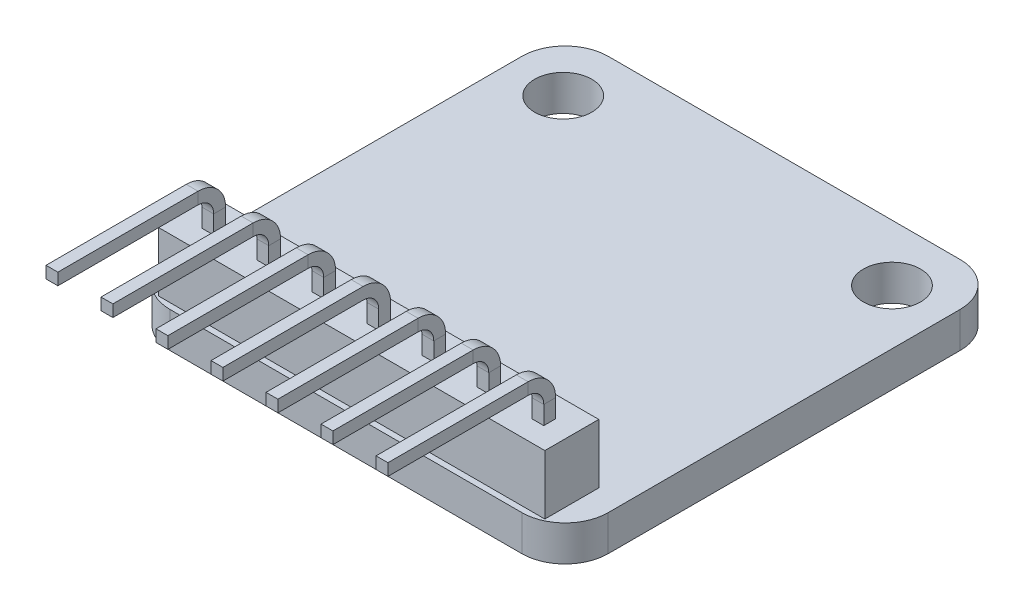
SolidWorks part; units mm, degrees
ref_plane "Front Plane" through (0, 0, 0) normal (0, 0, 1) x (1, 0, 0)
ref_plane "Top Plane" through (0, 0, 0) normal (0, 1, 0) x (1, 0, 0)
ref_plane "Right Plane" through (0, 0, 0) normal (1, 0, 0) x (0, 0, -1)
sketch "Sketch2" plane through (0, 0, 0) normal (0, 1, 0) x (1, 0, 0)
  line L0 (2.54, 17.695) -> (17.78, 17.695) construction
  line L1 (0, 0) -> (20.32, 0)
  line L2 (0, 0) -> (0, 20.32)
  line L3 (0, 20.32) -> (20.32, 20.32)
  line L4 (20.32, 0) -> (20.32, 20.32)
  circle A0 centre (2.54, 17.695) radius 1.325
  circle A1 centre (17.78, 17.695) radius 1.325
  point P7 (10.16, 17.695)
  point P8 (10.16, 20.32)
  dimension "D4" = 2.65
  dimension "D1" = 20.32
  dimension "D2" = 20.32
  dimension "D3" = 15.24
  dimension "D5" = 1.3
extrude "Boss-Extrude1" add sketch "Sketch2" along normal blind 1.65
sketch "Sketch3" plane through (0, 1.65, 0) normal (0, 1, 0) x (1, 0, 0)
  line L0 (0, 0) -> (20.32, 0) construction
  line L1 (9.885, 1.249) -> (10.435, 1.249)
  line L2 (9.885, 1.249) -> (9.885, 1.799)
  line L3 (9.885, 1.799) -> (10.435, 1.799)
  line L4 (10.435, 1.249) -> (10.435, 1.799)
  line L5 (9.885, 1.249) -> (10.435, 1.799) construction
  line L6 (9.885, 1.799) -> (10.435, 1.249) construction
  point P0 (10.16, 1.524)
  point P10 (10.16, 0)
  dimension "D1" = 0.55
  dimension "D2" = 1.524
sketch "Sketch4" plane through (0, 0, 0) normal (1, 0, 0) x (0, 0, -1)
  line L0 (1.524, 1.65) -> (1.524, 5.25)
  line L1 (0.524, 6.25) -> (-5.976, 6.25)
  arc A0 (1.524, 5.25) -> (0.524, 6.25) centre (0.524, 5.25) ccw
  point P6 (1.524, 6.25)
  dimension "D3" = 1
  dimension "D1" = 4.6
  dimension "D2" = 7.5
sweep "Sweep1" add profiles "Sketch3" path "Sketch4"
pattern_linear "LPattern1" count 4 spacing 2.55 along (-1, 0, 0) count 4 spacing 2.55 along (1, 0, 0) of "Sweep1"
sketch "Sketch5" plane through (0, 1.65, 0) normal (0, 1, 0) x (1, 0, 0)
  line L0 (2.235, 1.799) -> (2.235, 1.249) construction
  line L1 (1.21, 0.274) -> (19.11, 0.274)
  line L2 (1.21, 0.274) -> (1.21, 2.774)
  line L3 (1.21, 2.774) -> (19.11, 2.774)
  line L4 (19.11, 0.274) -> (19.11, 2.774)
  line L5 (0, 0) -> (20.32, 0) construction
  point P6 (2.235, 1.524)
  point P7 (1.21, 1.524)
  point P10 (10.16, 0)
  point P11 (10.16, 0.274)
  dimension "D1" = 17.9
  dimension "D2" = 2.5
extrude "Boss-Extrude2" add sketch "Sketch5" along normal blind 2.75
sketch "Sketch6" plane through (0, 0, 0) normal (0, -1, 0) x (1, 0, 0)
  line L0 (0, -20.32) -> (0, 0) construction
  line L1 (8.906, -8.656) -> (10.906, -8.656)
  line L2 (8.906, -8.656) -> (8.906, -11.156)
  line L3 (8.906, -11.156) -> (10.906, -11.156)
  line L4 (10.906, -8.656) -> (10.906, -11.156)
  line L5 (8.906, -8.656) -> (10.906, -11.156) construction
  line L6 (8.906, -11.156) -> (10.906, -8.656) construction
  line L7 (11.958, -8.656) -> (14.458, -8.656)
  line L8 (11.958, -8.656) -> (11.958, -12.156)
  line L9 (11.958, -12.156) -> (14.458, -12.156)
  line L10 (14.458, -8.656) -> (14.458, -12.156)
  line L11 (11.958, -8.656) -> (14.458, -12.156) construction
  line L12 (11.958, -12.156) -> (14.458, -8.656) construction
  line L13 (20.32, -20.32) -> (0, -20.32) construction
  point P0 (9.906, -9.906)
  point P5 (13.208, -10.406)
  dimension "D1" = 3.302
  dimension "D2" = 9.906
  dimension "D3" = 10.414
  dimension "D4" = 2
  dimension "D5" = 2.5
  dimension "D6" = 2.5
  dimension "D7" = 3.5
extrude "Boss-Extrude3" add sketch "Sketch6" along normal blind 0.5
fillet "Fillet1" radius 2 4 edges at (0, 0.825, 0) (0, 0.825, -20.32) (20.32, 0.825, -20.32) (20.32, 0.825, 0)
sketch "Sketch7" plane through (0, -0.5, 0) normal (0, -1, 0) x (1, 0, 0)
  line L8 (14.058, -11.756) -> (14.058, -9.056)
  line L9 (14.058, -9.056) -> (12.358, -9.056)
  line L10 (12.358, -9.056) -> (12.358, -11.756)
  line L11 (12.358, -11.756) -> (14.058, -11.756)
  line L12 (14.058, -11.756) -> (14.058, -9.056)
  line L13 (14.058, -9.056) -> (12.358, -9.056)
  line L14 (12.358, -9.056) -> (12.358, -11.756)
  line L15 (12.358, -11.756) -> (14.058, -11.756)
  dimension "D1" = 0.4
extrude "Cut-Extrude1" cut sketch "Sketch7" against normal blind 0.1
equation "\"width\"= 24"
equation "\"thk\"= 3"
equation "\"holesize\"= 4.2"
equation "\"holedistance\"= ( 20 + 12 ) / 2"
equation "\"threaded_hole\"= 3.9"
equation "\"fillet_radius\"= 2"
equation "\"ground_clearance\"= 25"
equation "\"tire_thk\"= 3"
equation "\"innerwheel_diam\" = \"wheel_diam\"-2*\"tire_thk\""
equation "\"innerwheel_thk\"= 8"
equation "\"wheel_diam\"= 2*(\"width\"/2+\"ground_clearance\")"
equation "\"coloursensor_holesize\"= 2.65"
equation "\"D4@Sketch2\"=\"coloursensor_holesize\""
equation "\"hole_to_edge\" = 4"
